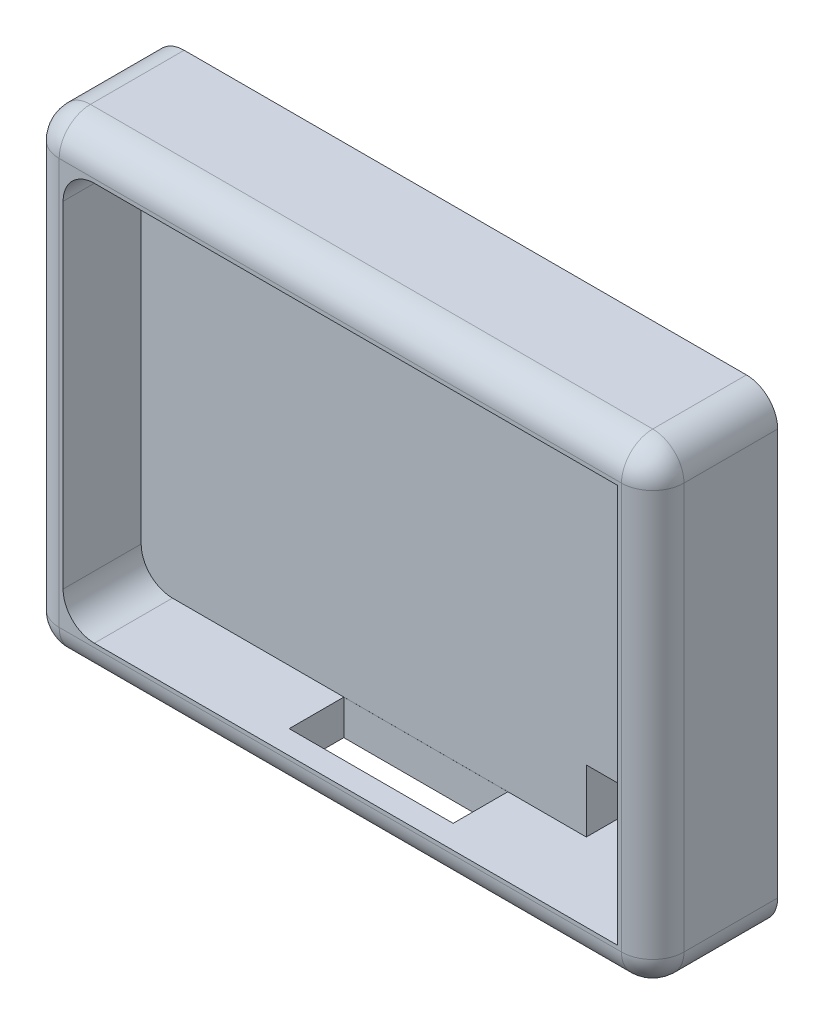
SolidWorks part; units mm, degrees
ref_plane "前视基准面" through (0, 0, 0) normal (0, 0, 1) x (1, 0, 0)
ref_plane "上视基准面" through (0, 0, 0) normal (0, 1, 0) x (1, 0, 0)
ref_plane "右视基准面" through (0, 0, 0) normal (1, 0, 0) x (0, 0, -1)
sketch "Sketch1" plane through (0, 0, 0) normal (0, 0, 1) x (1, 0, 0)
  line L0 (20, 30) -> (20, 0) construction
  line L1 (0, 0) -> (40, 0)
  line L2 (0, 0) -> (0, 30)
  line L3 (0, 30) -> (40, 30)
  line L4 (40, 0) -> (40, 30)
  line L5 (0, 15) -> (40, 15) construction
  point P9 (20, 15)
  dimension "D1" = 40
  dimension "D2" = 30
extrude "Boss-Extrude1" add sketch "Sketch1" along normal blind 8
sketch "Sketch2" plane through (0, 0, 8) normal (0, 0, 1) x (1, 0, 0)
  line L0 (0, 30) -> (40, 0) construction
  line L1 (0, 0) -> (40, 0) construction
  line L2 (40, 0) -> (40, 30) construction
  line L3 (40, 30) -> (0, 0) construction
  line L5 (2.25, 27.75) -> (37.75, 27.75)
  line L6 (2.25, 27.75) -> (2.25, 2.25)
  line L7 (2.25, 2.25) -> (37.75, 2.25)
  line L8 (37.75, 27.75) -> (37.75, 2.25)
  line L9 (2.25, 27.75) -> (37.75, 2.25) construction
  line L10 (2.25, 2.25) -> (37.75, 27.75) construction
  point P11 (20, 15)
  dimension "D1" = 35.5
  dimension "D2" = 25.5
extrude "Cut-Extrude1" cut sketch "Sketch2" against normal blind 5
fillet "Fillet1" radius 2 2 edges at (2.25, 27.75, 5.5) (2.25, 2.25, 5.5)
fillet "Fillet2" radius 2 8 edges at (20, 0, 8) (40, 15, 8) (20, 30, 8) (0, 15, 8) (0, 0, 4) (40, 0, 4) (40, 30, 4) (0, 30, 4)
sketch "Sketch3" plane through (0, 0, 3) normal (0, 0, 1) x (1, 0, 0)
  line L1 (37.75, 2.25) -> (30.75, 2.25)
  line L2 (37.75, 2.25) -> (37.75, 6.25)
  line L3 (37.75, 6.25) -> (30.75, 6.25)
  line L4 (30.75, 2.25) -> (30.75, 6.25)
  dimension "D1" = 7
  dimension "D2" = 4
extrude "Cut-Extrude2" cut sketch "Sketch3" against normal up to surface (3 mm away) up to face at (20, 15, 0)
sketch "Sketch6" plane through (0, 2.25, 0) normal (0, 1, 0) x (1, 0, 0)
  line L0 (30.75, -3) -> (37.75, -3) construction
  line L1 (37.75, 0) -> (37.75, -8) construction
  line L2 (37.75, -3) -> (37.75, -4.7524) construction
  line L3 (37.75, -4.7524) -> (20.4758, -4.7524) construction
  line L4 (4.25, -3) -> (30.75, -3) construction
  line L6 (15.2258, -3.0024) -> (25.7258, -3.0024)
  line L7 (15.2258, -3.0024) -> (15.2258, -6.5024)
  line L8 (15.2258, -6.5024) -> (25.7258, -6.5024)
  line L9 (25.7258, -3.0024) -> (25.7258, -6.5024)
  line L10 (15.2258, -3.0024) -> (25.7258, -6.5024) construction
  line L11 (15.2258, -6.5024) -> (25.7258, -3.0024) construction
  dimension "D1" = 3.5
  dimension "D2" = 10.5
extrude "Cut-Extrude3" cut sketch "Sketch6" against normal up to surface (2.25 mm away) up to face at (20, 0, 3)
